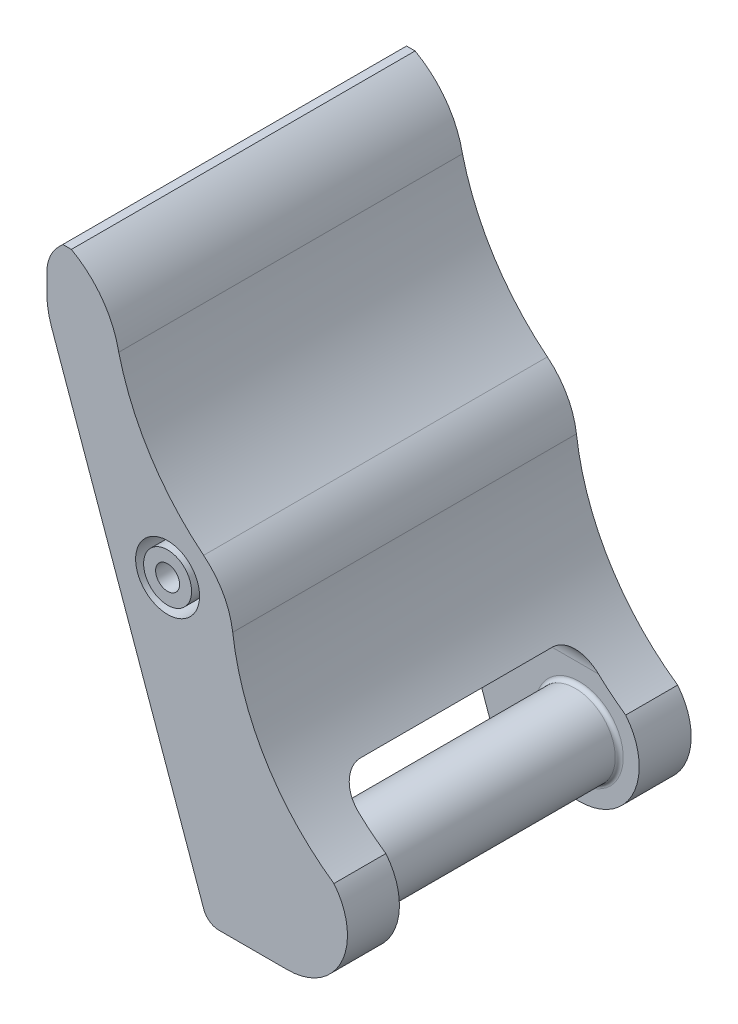
SolidWorks part; units mm, degrees
ref_plane "前视基准面" through (0, 0, 0) normal (0, 0, 1) x (1, 0, 0)
ref_plane "上视基准面" through (0, 0, 0) normal (0, 1, 0) x (1, 0, 0)
ref_plane "右视基准面" through (0, 0, 0) normal (1, 0, 0) x (0, 0, -1)
sketch "草图1" plane through (0, 0, 0) normal (0, 0, 1) x (1, 0, 0)
  line L0 (-65.3484, 0) -> (67.3408, 0) construction
  line L1 (0, 56.0841) -> (0, -64.0534) construction
  line L2 (0, 0) -> (10, 0)
  line L3 (0, 0) -> (-20.1078, 56.5303)
  line L4 (-20.1078, 56.5303) -> (-20.1078, 64.5303)
  line L5 (-20.1078, 64.5303) -> (-17.0359, 64.5303)
  arc A0 (10, 0) -> (15.8034, 12.2509) centre (10, 7.5) ccw
  arc A2 (-17.0359, 64.5303) -> (-11.112, 56.3492) centre (-22.8907, 54.0556) cw
  arc A3 (-11.112, 56.3492) -> (-0.4928, 39.6585) centre (18.9856, 63.7748) ccw
  arc A4 (3.1449, 33.1336) -> (15.8034, 12.2509) centre (32.9079, 36.8971) ccw
  arc A5 (-0.4928, 39.6585) -> (3.1449, 33.1336) centre (-6.7761, 31.8791) cw
  dimension "D2" = 15
  dimension "D5" = 12
  dimension "D6" = 31
  dimension "D7" = 30
  dimension "D8" = 10
  dimension "D1" = 10
  dimension "D3" = 60
  dimension "D4" = 8
extrude "凸台-拉伸1" add sketch "草图1" along normal mid plane 43
fillet "圆角1" radius 10 1 edges at (-20.1078, 56.5303, 0)
fillet "圆角2" radius 2 1 edges at (0, 0, 0)
chamfer "倒角1" distance 2 angle 45 1 edges at (-20.1078, 64.5303, 0)
fillet "圆角3" radius 5 1 edges at (-20.1078, 62.5303, 0)
ref_plane "基准面1" through (20, 0, 0) normal (1, 0, 0) x (0, 0, -1)
sketch "草图4" plane through (20, 0, 0) normal (1, 0, 0) x (0, 0, -1)
  line L0 (0, 79.267) -> (0, -14.4581) construction
  line L1 (-15, 0) -> (-15, 18)
  line L2 (-15, 18) -> (15, 18)
  line L3 (15, 18) -> (15, 0)
  line L4 (15, 0) -> (-15, 0)
  line L5 (-21.5, 0) -> (21.5, 0) construction
  dimension "D1" = 6.5
  dimension "D2" = 6.5
  dimension "D3" = 18
extrude "切除-拉伸1" cut sketch "草图4" against normal through all
fillet "圆角4" radius 3 2 edges at (1.6025, 18, 15) (1.6025, 18, -15)
sketch "草图5" plane through (0, 0, -15) normal (0, 0, 1) x (1, 0, 0)
  circle A0 centre (10, 7.5) radius 5
  dimension "D1" = 10
extrude "凸台-拉伸2" add sketch "草图5" along normal blind 30
fillet "圆角5" radius 0.5 2 edges at (10, 2.5, 15) (10, 12.5, -15)
sketch "草图6" plane through (0, 0, 0) normal (-0.9422, -0.3351, 0) x (0, 0, 1)
  line L0 (-9, 38.2745) -> (9, 38.2745) construction
  line L1 (-9, 44.2745) -> (9, 44.2745)
  line L2 (-9, 32.2745) -> (9, 32.2745)
  line L3 (0, 73.5526) -> (0, -21.9816) construction
  line L4 (21.5, 58.2745) -> (-21.5, 58.2745) construction
  arc A0 (-9, 44.2745) -> (-9, 32.2745) centre (-9, 38.2745) ccw
  arc A1 (9, 32.2745) -> (9, 44.2745) centre (9, 38.2745) ccw
  point P2 (0, 38.2745)
  dimension "D1" = 6
  dimension "D2" = 18
  dimension "D3" = 20
extrude "切除-拉伸2" cut sketch "草图6" against normal blind 1
sketch "草图7" plane through (0.9422, 0.3351, 0) normal (-0.9422, -0.3351, 0) x (0, 0, 1)
  line L0 (-9, 32.2745) -> (9, 32.2745) construction
  text T0 "SHARK" font "汉仪长仿宋体" height 3.5
  dimension "D1" = 4
extrude "凸台-拉伸3" add sketch "草图7" along normal blind 1
sketch "草图8" plane through (0, 0, 21.5) normal (0, 0, 1) x (1, 0, 0)
  circle A0 centre (-5, 35) radius 1.5
  dimension "D1" = 3
  dimension "D2" = 35
  dimension "D3" = 5
extrude "切除-拉伸3" cut sketch "草图8" against normal through all
sketch "草图9" plane through (0, 0, 21.5) normal (0, 0, 1) x (1, 0, 0)
  circle A0 centre (-5, 35) radius 3
  circle A1 centre (-5, 35) radius 4
  dimension "D1" = 6
  dimension "D2" = 8
extrude "切除-拉伸4" cut sketch "草图9" against normal blind 5
mirror "镜向1" about plane through (0, 0, 0) normal (0, 0, 1) of "切除-拉伸4"
